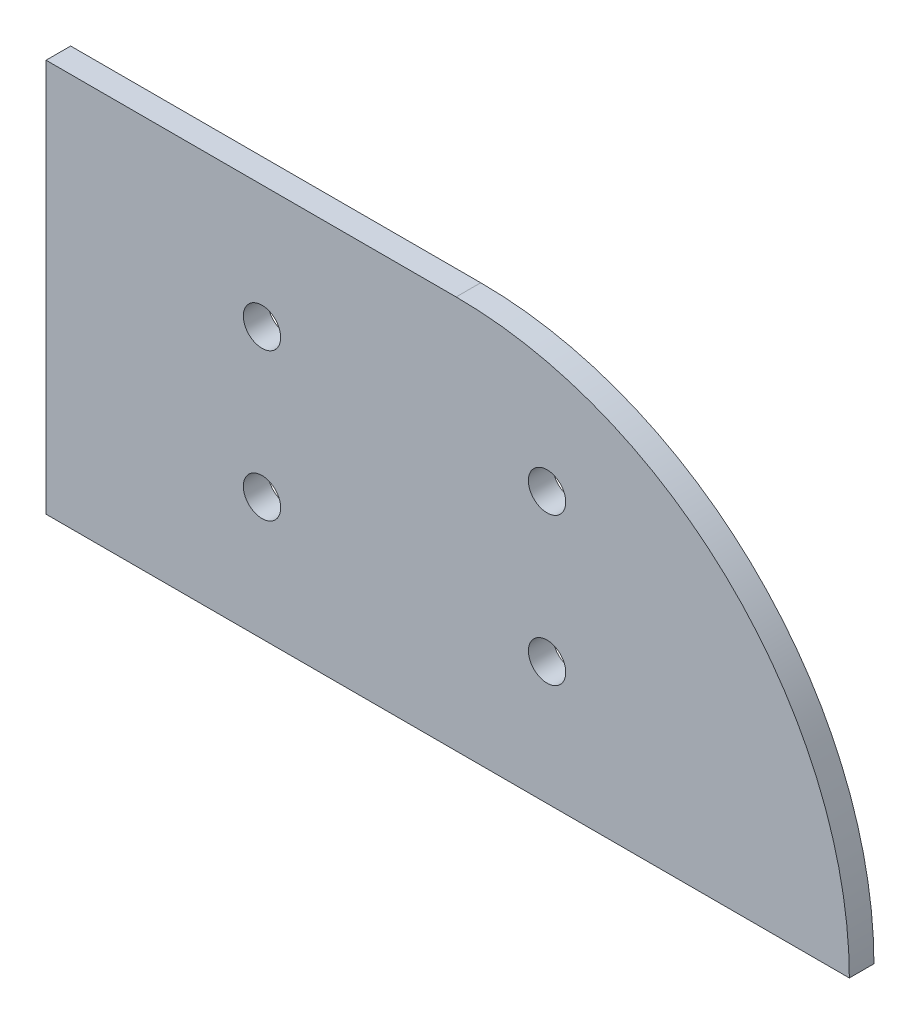
SolidWorks part; units mm, degrees
ref_plane "Front Plane" through (0, 0, 0) normal (0, 0, 1) x (1, 0, 0)
ref_plane "Top Plane" through (0, 0, 0) normal (0, 1, 0) x (1, 0, 0)
ref_plane "Right Plane" through (0, 0, 0) normal (1, 0, 0) x (0, 0, -1)
sketch "Sketch1" plane through (0, 0, 0) normal (0, 0, 1) x (1, 0, 0)
  line L0 (0, 50.8) -> (0, 0)
  line L1 (0, 0) -> (103.779, 0)
  line L3 (52.979, 50.8) -> (0, 50.8)
  arc A0 (103.779, 0) -> (52.979, 50.8) centre (52.979, 0) ccw
  point P5 (88.9, 35.921)
  dimension "D1" = 88.9
  dimension "D2" = 50.8
  dimension "D3" = 103.779
extrude "Boss-Extrude1" add sketch "Sketch1" along normal blind 3.175
sketch "Sketch3" plane through (0, 0, 3.175) normal (0, 0, 1) x (1, 0, 0)
  line L0 (64.7265, 15.875) -> (54.5665, 15.875) construction
  line L1 (64.7265, 34.925) -> (54.5665, 34.925) construction
  circle A0 centre (64.7265, 15.875) radius 2.413 construction
  circle A1 centre (64.7265, 34.925) radius 2.413 construction
  circle A2 centre (27.8965, 15.875) radius 2.413 construction
  circle A3 centre (27.8965, 34.925) radius 2.413 construction
  circle A4 centre (64.7265, 15.875) radius 2.413
  circle A5 centre (64.7265, 34.925) radius 2.413
  circle A6 centre (27.8965, 15.875) radius 2.413
  circle A7 centre (27.8965, 34.925) radius 2.413
  circle A8 centre (54.5665, 34.925) radius 2.413
  circle A9 centre (54.5665, 15.875) radius 2.413
  dimension "D1" = 10.16
extrude "Cut-Extrude1" cut sketch "Sketch3" against normal through all and the other way through all contours A5 | A7 | A6 | A4
